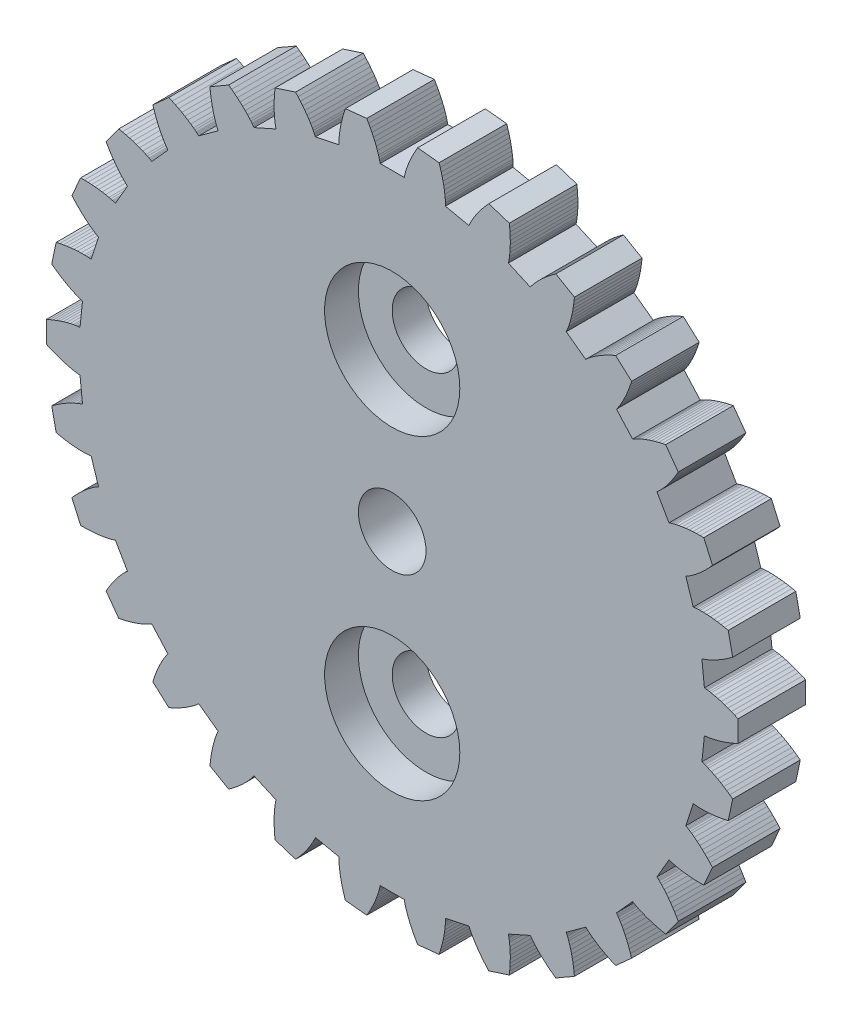
SolidWorks part; units mm, degrees
ref_plane "Front Plane" through (0, 0, 0) normal (0, 0, 1) x (1, 0, 0)
ref_plane "Top Plane" through (0, 0, 0) normal (0, 1, 0) x (1, 0, 0)
ref_plane "Right Plane" through (0, 0, 0) normal (1, 0, 0) x (0, 0, -1)
sketch "Model" plane through (0, 0, 0) normal (0, 0, 1) x (1, 0, 0)
  line L0 (29.209, 16.2732) -> (29.246, 16.2699)
  line L1 (29.246, 16.2699) -> (29.2831, 16.266)
  line L2 (29.2831, 16.266) -> (29.3202, 16.2615)
  line L3 (29.3202, 16.2615) -> (29.3573, 16.2565)
  line L4 (29.3573, 16.2565) -> (29.4317, 16.245)
  line L5 (29.4317, 16.245) -> (29.5061, 16.2317)
  line L6 (29.5061, 16.2317) -> (29.6552, 16.2001)
  line L7 (29.6552, 16.2001) -> (29.8045, 16.1625)
  line L8 (29.8045, 16.1625) -> (29.954, 16.1194)
  line L9 (29.954, 16.1194) -> (30.1035, 16.0712)
  line L10 (30.1035, 16.0712) -> (30.2531, 16.0181)
  line L11 (30.2531, 16.0181) -> (30.4025, 15.9603)
  line L12 (30.4025, 15.9603) -> (30.5519, 15.8981)
  line L13 (30.5519, 15.8981) -> (30.7012, 15.8315)
  line L14 (30.7012, 15.8315) -> (30.7012, 14.8771)
  line L15 (30.7012, 14.8771) -> (30.5519, 14.8105)
  line L16 (30.5519, 14.8105) -> (30.4025, 14.7482)
  line L17 (30.4025, 14.7482) -> (30.2531, 14.6905)
  line L18 (30.2531, 14.6905) -> (30.1035, 14.6374)
  line L19 (30.1035, 14.6374) -> (29.954, 14.5891)
  line L20 (29.954, 14.5891) -> (29.8045, 14.5461)
  line L21 (29.8045, 14.5461) -> (29.6552, 14.5085)
  line L22 (29.6552, 14.5085) -> (29.5061, 14.4769)
  line L23 (29.5061, 14.4769) -> (29.4317, 14.4636)
  line L24 (29.4317, 14.4636) -> (29.3573, 14.4521)
  line L25 (29.3573, 14.4521) -> (29.3202, 14.4471)
  line L26 (29.3202, 14.4471) -> (29.2831, 14.4426)
  line L27 (29.2831, 14.4426) -> (29.246, 14.4387)
  line L28 (29.246, 14.4387) -> (29.209, 14.4354)
  line L29 (29.209, 14.4354) -> (29.0973, 13.3725)
  line L30 (29.0973, 13.3725) -> (29.1328, 13.3616)
  line L31 (29.1328, 13.3616) -> (29.1683, 13.3501)
  line L32 (29.1683, 13.3501) -> (29.2036, 13.338)
  line L33 (29.2036, 13.338) -> (29.2389, 13.3254)
  line L34 (29.2389, 13.3254) -> (29.3092, 13.2987)
  line L35 (29.3092, 13.2987) -> (29.3793, 13.2702)
  line L36 (29.3793, 13.2702) -> (29.5185, 13.2083)
  line L37 (29.5185, 13.2083) -> (29.6568, 13.1405)
  line L38 (29.6568, 13.1405) -> (29.794, 13.0673)
  line L39 (29.794, 13.0673) -> (29.9303, 12.989)
  line L40 (29.9303, 12.989) -> (30.0655, 12.906)
  line L41 (30.0655, 12.906) -> (30.1997, 12.8184)
  line L42 (30.1997, 12.8184) -> (30.3329, 12.7264)
  line L43 (30.3329, 12.7264) -> (30.465, 12.6303)
  line L44 (30.465, 12.6303) -> (30.2666, 11.6967)
  line L45 (30.2666, 11.6967) -> (30.1068, 11.6626)
  line L46 (30.1068, 11.6626) -> (29.9477, 11.6328)
  line L47 (29.9477, 11.6328) -> (29.7895, 11.6074)
  line L48 (29.7895, 11.6074) -> (29.6321, 11.5865)
  line L49 (29.6321, 11.5865) -> (29.4759, 11.5704)
  line L50 (29.4759, 11.5704) -> (29.3207, 11.5594)
  line L51 (29.3207, 11.5594) -> (29.1668, 11.5536)
  line L52 (29.1668, 11.5536) -> (29.0144, 11.5537)
  line L53 (29.0144, 11.5537) -> (28.9389, 11.5562)
  line L54 (28.9389, 11.5562) -> (28.8637, 11.5604)
  line L55 (28.8637, 11.5604) -> (28.8264, 11.5632)
  line L56 (28.8264, 11.5632) -> (28.7892, 11.5666)
  line L57 (28.7892, 11.5666) -> (28.7521, 11.5704)
  line L58 (28.7521, 11.5704) -> (28.7152, 11.5749)
  line L59 (28.7152, 11.5749) -> (28.3849, 10.5585)
  line L60 (28.3849, 10.5585) -> (28.4174, 10.5404)
  line L61 (28.4174, 10.5404) -> (28.4497, 10.5218)
  line L62 (28.4497, 10.5218) -> (28.4818, 10.5026)
  line L63 (28.4818, 10.5026) -> (28.5137, 10.4829)
  line L64 (28.5137, 10.4829) -> (28.5769, 10.4422)
  line L65 (28.5769, 10.4422) -> (28.6395, 10.3998)
  line L66 (28.6395, 10.3998) -> (28.7628, 10.3103)
  line L67 (28.7628, 10.3103) -> (28.884, 10.2152)
  line L68 (28.884, 10.2152) -> (29.003, 10.115)
  line L69 (29.003, 10.115) -> (29.12, 10.0102)
  line L70 (29.12, 10.0102) -> (29.235, 9.9008)
  line L71 (29.235, 9.9008) -> (29.3481, 9.7873)
  line L72 (29.3481, 9.7873) -> (29.4592, 9.6696)
  line L73 (29.4592, 9.6696) -> (29.5684, 9.5481)
  line L74 (29.5684, 9.5481) -> (29.1802, 8.6762)
  line L75 (29.1802, 8.6762) -> (29.0168, 8.6761)
  line L76 (29.0168, 8.6761) -> (28.8551, 8.68)
  line L77 (28.8551, 8.68) -> (28.695, 8.688)
  line L78 (28.695, 8.688) -> (28.5368, 8.7003)
  line L79 (28.5368, 8.7003) -> (28.3806, 8.7171)
  line L80 (28.3806, 8.7171) -> (28.2265, 8.7385)
  line L81 (28.2265, 8.7385) -> (28.0748, 8.7649)
  line L82 (28.0748, 8.7649) -> (27.9257, 8.7967)
  line L83 (27.9257, 8.7967) -> (27.8523, 8.8148)
  line L84 (27.8523, 8.8148) -> (27.7797, 8.8345)
  line L85 (27.7797, 8.8345) -> (27.7438, 8.8451)
  line L86 (27.7438, 8.8451) -> (27.7081, 8.8561)
  line L87 (27.7081, 8.8561) -> (27.6726, 8.8676)
  line L88 (27.6726, 8.8676) -> (27.6375, 8.8796)
  line L89 (27.6375, 8.8796) -> (27.1031, 7.9541)
  line L90 (27.1031, 7.9541) -> (27.1311, 7.9296)
  line L91 (27.1311, 7.9296) -> (27.1588, 7.9047)
  line L92 (27.1588, 7.9047) -> (27.1862, 7.8793)
  line L93 (27.1862, 7.8793) -> (27.2133, 7.8534)
  line L94 (27.2133, 7.8534) -> (27.2667, 7.8004)
  line L95 (27.2667, 7.8004) -> (27.3191, 7.7459)
  line L96 (27.3191, 7.7459) -> (27.4211, 7.6327)
  line L97 (27.4211, 7.6327) -> (27.5198, 7.5145)
  line L98 (27.5198, 7.5145) -> (27.6154, 7.3918)
  line L99 (27.6154, 7.3918) -> (27.708, 7.2649)
  line L100 (27.708, 7.2649) -> (27.7978, 7.134)
  line L101 (27.7978, 7.134) -> (27.8848, 6.9994)
  line L102 (27.8848, 6.9994) -> (27.9691, 6.8613)
  line L103 (27.9691, 6.8613) -> (28.0507, 6.7197)
  line L104 (28.0507, 6.7197) -> (27.4897, 5.9476)
  line L105 (27.4897, 5.9476) -> (27.3298, 5.9814)
  line L106 (27.3298, 5.9814) -> (27.1724, 6.0188)
  line L107 (27.1724, 6.0188) -> (27.0175, 6.06)
  line L108 (27.0175, 6.06) -> (26.8653, 6.1049)
  line L109 (26.8653, 6.1049) -> (26.7159, 6.1538)
  line L110 (26.7159, 6.1538) -> (26.5697, 6.2068)
  line L111 (26.5697, 6.2068) -> (26.4268, 6.2641)
  line L112 (26.4268, 6.2641) -> (26.2876, 6.3262)
  line L113 (26.2876, 6.3262) -> (26.2196, 6.3592)
  line L114 (26.2196, 6.3592) -> (26.1527, 6.3936)
  line L115 (26.1527, 6.3936) -> (26.1197, 6.4114)
  line L116 (26.1197, 6.4114) -> (26.0871, 6.4296)
  line L117 (26.0871, 6.4296) -> (26.0548, 6.4482)
  line L118 (26.0548, 6.4482) -> (26.0229, 6.4673)
  line L119 (26.0229, 6.4673) -> (25.3078, 5.6731)
  line L120 (25.3078, 5.6731) -> (25.3301, 5.6433)
  line L121 (25.3301, 5.6433) -> (25.352, 5.6132)
  line L122 (25.352, 5.6132) -> (25.3735, 5.5826)
  line L123 (25.3735, 5.5826) -> (25.3946, 5.5517)
  line L124 (25.3946, 5.5517) -> (25.4358, 5.4888)
  line L125 (25.4358, 5.4888) -> (25.4757, 5.4245)
  line L126 (25.4757, 5.4245) -> (25.552, 5.2926)
  line L127 (25.552, 5.2926) -> (25.624, 5.1565)
  line L128 (25.624, 5.1565) -> (25.692, 5.0166)
  line L129 (25.692, 5.0166) -> (25.7562, 4.8732)
  line L130 (25.7562, 4.8732) -> (25.8168, 4.7265)
  line L131 (25.8168, 4.7265) -> (25.8739, 4.5768)
  line L132 (25.8739, 4.5768) -> (25.9276, 4.4241)
  line L133 (25.9276, 4.4241) -> (25.978, 4.2687)
  line L134 (25.978, 4.2687) -> (25.2687, 3.63)
  line L135 (25.2687, 3.63) -> (25.1194, 3.6964)
  line L136 (25.1194, 3.6964) -> (24.9732, 3.7657)
  line L137 (24.9732, 3.7657) -> (24.8302, 3.8382)
  line L138 (24.8302, 3.8382) -> (24.6907, 3.9138)
  line L139 (24.6907, 3.9138) -> (24.5548, 3.9926)
  line L140 (24.5548, 3.9926) -> (24.4227, 4.0749)
  line L141 (24.4227, 4.0749) -> (24.2949, 4.1607)
  line L142 (24.2949, 4.1607) -> (24.1717, 4.2503)
  line L143 (24.1717, 4.2503) -> (24.112, 4.2968)
  line L144 (24.112, 4.2968) -> (24.0537, 4.3443)
  line L145 (24.0537, 4.3443) -> (24.0251, 4.3685)
  line L146 (24.0251, 4.3685) -> (23.997, 4.3931)
  line L147 (23.997, 4.3931) -> (23.9693, 4.4181)
  line L148 (23.9693, 4.4181) -> (23.9421, 4.4434)
  line L149 (23.9421, 4.4434) -> (23.0774, 3.8152)
  line L150 (23.0774, 3.8152) -> (23.0931, 3.7815)
  line L151 (23.0931, 3.7815) -> (23.1082, 3.7474)
  line L152 (23.1082, 3.7474) -> (23.1229, 3.7131)
  line L153 (23.1229, 3.7131) -> (23.1371, 3.6784)
  line L154 (23.1371, 3.6784) -> (23.1644, 3.6083)
  line L155 (23.1644, 3.6083) -> (23.19, 3.5372)
  line L156 (23.19, 3.5372) -> (23.2372, 3.3922)
  line L157 (23.2372, 3.3922) -> (23.2793, 3.2441)
  line L158 (23.2793, 3.2441) -> (23.3168, 3.0932)
  line L159 (23.3168, 3.0932) -> (23.3498, 2.9395)
  line L160 (23.3498, 2.9395) -> (23.3785, 2.7835)
  line L161 (23.3785, 2.7835) -> (23.4033, 2.6251)
  line L162 (23.4033, 2.6251) -> (23.4241, 2.4646)
  line L163 (23.4241, 2.4646) -> (23.441, 2.3021)
  line L164 (23.441, 2.3021) -> (22.6144, 1.8249)
  line L165 (22.6144, 1.8249) -> (22.4822, 1.9208)
  line L166 (22.4822, 1.9208) -> (22.3536, 2.0191)
  line L167 (22.3536, 2.0191) -> (22.2288, 2.1197)
  line L168 (22.2288, 2.1197) -> (22.108, 2.2226)
  line L169 (22.108, 2.2226) -> (21.9915, 2.328)
  line L170 (21.9915, 2.328) -> (21.8795, 2.4359)
  line L171 (21.8795, 2.4359) -> (21.7722, 2.5464)
  line L172 (21.7722, 2.5464) -> (21.6703, 2.6598)
  line L173 (21.6703, 2.6598) -> (21.6216, 2.7176)
  line L174 (21.6216, 2.7176) -> (21.5745, 2.7762)
  line L175 (21.5745, 2.7762) -> (21.5516, 2.8058)
  line L176 (21.5516, 2.8058) -> (21.5292, 2.8357)
  line L177 (21.5292, 2.8357) -> (21.5072, 2.8659)
  line L178 (21.5072, 2.8659) -> (21.4859, 2.8963)
  line L179 (21.4859, 2.8963) -> (20.5095, 2.4616)
  line L180 (20.5095, 2.4616) -> (20.5178, 2.4254)
  line L181 (20.5178, 2.4254) -> (20.5256, 2.3889)
  line L182 (20.5256, 2.3889) -> (20.5328, 2.3523)
  line L183 (20.5328, 2.3523) -> (20.5395, 2.3154)
  line L184 (20.5395, 2.3154) -> (20.5516, 2.2411)
  line L185 (20.5516, 2.2411) -> (20.5619, 2.1662)
  line L186 (20.5619, 2.1662) -> (20.5779, 2.0147)
  line L187 (20.5779, 2.0147) -> (20.5883, 1.8611)
  line L188 (20.5883, 1.8611) -> (20.5935, 1.7056)
  line L189 (20.5935, 1.7056) -> (20.5939, 1.5485)
  line L190 (20.5939, 1.5485) -> (20.5896, 1.3898)
  line L191 (20.5896, 1.3898) -> (20.5808, 1.2298)
  line L192 (20.5808, 1.2298) -> (20.5678, 1.0685)
  line L193 (20.5678, 1.0685) -> (20.5506, 0.906)
  line L194 (20.5506, 0.906) -> (19.6429, 0.6111)
  line L195 (19.6429, 0.6111) -> (19.5334, 0.7324)
  line L196 (19.5334, 0.7324) -> (19.4281, 0.8553)
  line L197 (19.4281, 0.8553) -> (19.3269, 0.9796)
  line L198 (19.3269, 0.9796) -> (19.2302, 1.1054)
  line L199 (19.2302, 1.1054) -> (19.1381, 1.2327)
  line L200 (19.1381, 1.2327) -> (19.051, 1.3615)
  line L201 (19.051, 1.3615) -> (18.9691, 1.4919)
  line L202 (18.9691, 1.4919) -> (18.893, 1.624)
  line L203 (18.893, 1.624) -> (18.8573, 1.6907)
  line L204 (18.8573, 1.6907) -> (18.8234, 1.7578)
  line L205 (18.8234, 1.7578) -> (18.8072, 1.7916)
  line L206 (18.8072, 1.7916) -> (18.7915, 1.8255)
  line L207 (18.7915, 1.8255) -> (18.7763, 1.8595)
  line L208 (18.7763, 1.8595) -> (18.7617, 1.8937)
  line L209 (18.7617, 1.8937) -> (17.7163, 1.6715)
  line L210 (17.7163, 1.6715) -> (17.7169, 1.6343)
  line L211 (17.7169, 1.6343) -> (17.7169, 1.5971)
  line L212 (17.7169, 1.5971) -> (17.7164, 1.5597)
  line L213 (17.7164, 1.5597) -> (17.7153, 1.5223)
  line L214 (17.7153, 1.5223) -> (17.7116, 1.4471)
  line L215 (17.7116, 1.4471) -> (17.7061, 1.3717)
  line L216 (17.7061, 1.3717) -> (17.6903, 1.2201)
  line L217 (17.6903, 1.2201) -> (17.6685, 1.0677)
  line L218 (17.6685, 1.0677) -> (17.6413, 0.9146)
  line L219 (17.6413, 0.9146) -> (17.609, 0.7608)
  line L220 (17.609, 0.7608) -> (17.5718, 0.6065)
  line L221 (17.5718, 0.6065) -> (17.53, 0.4518)
  line L222 (17.53, 0.4518) -> (17.4837, 0.2967)
  line L223 (17.4837, 0.2967) -> (17.4331, 0.1414)
  line L224 (17.4331, 0.1414) -> (16.4839, 0.0416)
  line L225 (16.4839, 0.0416) -> (16.402, 0.183)
  line L226 (16.402, 0.183) -> (16.3245, 0.3251)
  line L227 (16.3245, 0.3251) -> (16.2515, 0.4677)
  line L228 (16.2515, 0.4677) -> (16.183, 0.6109)
  line L229 (16.183, 0.6109) -> (16.1194, 0.7546)
  line L230 (16.1194, 0.7546) -> (16.0609, 0.8987)
  line L231 (16.0609, 0.8987) -> (16.008, 1.0433)
  line L232 (16.008, 1.0433) -> (15.961, 1.1883)
  line L233 (15.961, 1.1883) -> (15.9399, 1.2609)
  line L234 (15.9399, 1.2609) -> (15.9207, 1.3336)
  line L235 (15.9207, 1.3336) -> (15.9119, 1.3701)
  line L236 (15.9119, 1.3701) -> (15.9036, 1.4065)
  line L237 (15.9036, 1.4065) -> (15.8958, 1.4429)
  line L238 (15.8958, 1.4429) -> (15.8887, 1.4794)
  line L239 (15.8887, 1.4794) -> (14.8199, 1.4794)
  line L240 (14.8199, 1.4794) -> (14.8128, 1.4429)
  line L241 (14.8128, 1.4429) -> (14.805, 1.4065)
  line L242 (14.805, 1.4065) -> (14.7967, 1.3701)
  line L243 (14.7967, 1.3701) -> (14.7878, 1.3336)
  line L244 (14.7878, 1.3336) -> (14.7686, 1.2609)
  line L245 (14.7686, 1.2609) -> (14.7476, 1.1883)
  line L246 (14.7476, 1.1883) -> (14.7006, 1.0433)
  line L247 (14.7006, 1.0433) -> (14.6476, 0.8987)
  line L248 (14.6476, 0.8987) -> (14.5891, 0.7546)
  line L249 (14.5891, 0.7546) -> (14.5256, 0.6109)
  line L250 (14.5256, 0.6109) -> (14.4571, 0.4677)
  line L251 (14.4571, 0.4677) -> (14.384, 0.3251)
  line L252 (14.384, 0.3251) -> (14.3065, 0.183)
  line L253 (14.3065, 0.183) -> (14.2247, 0.0416)
  line L254 (14.2247, 0.0416) -> (13.2755, 0.1414)
  line L255 (13.2755, 0.1414) -> (13.2249, 0.2967)
  line L256 (13.2249, 0.2967) -> (13.1786, 0.4518)
  line L257 (13.1786, 0.4518) -> (13.1368, 0.6065)
  line L258 (13.1368, 0.6065) -> (13.0996, 0.7608)
  line L259 (13.0996, 0.7608) -> (13.0673, 0.9146)
  line L260 (13.0673, 0.9146) -> (13.04, 1.0677)
  line L261 (13.04, 1.0677) -> (13.0183, 1.2201)
  line L262 (13.0183, 1.2201) -> (13.0024, 1.3717)
  line L263 (13.0024, 1.3717) -> (12.997, 1.4471)
  line L264 (12.997, 1.4471) -> (12.9933, 1.5223)
  line L265 (12.9933, 1.5223) -> (12.9922, 1.5597)
  line L266 (12.9922, 1.5597) -> (12.9916, 1.5971)
  line L267 (12.9916, 1.5971) -> (12.9916, 1.6343)
  line L268 (12.9916, 1.6343) -> (12.9922, 1.6715)
  line L269 (12.9922, 1.6715) -> (11.9468, 1.8937)
  line L270 (11.9468, 1.8937) -> (11.9323, 1.8595)
  line L271 (11.9323, 1.8595) -> (11.9171, 1.8255)
  line L272 (11.9171, 1.8255) -> (11.9014, 1.7916)
  line L273 (11.9014, 1.7916) -> (11.8852, 1.7578)
  line L274 (11.8852, 1.7578) -> (11.8513, 1.6907)
  line L275 (11.8513, 1.6907) -> (11.8156, 1.624)
  line L276 (11.8156, 1.624) -> (11.7395, 1.4919)
  line L277 (11.7395, 1.4919) -> (11.6576, 1.3615)
  line L278 (11.6576, 1.3615) -> (11.5704, 1.2327)
  line L279 (11.5704, 1.2327) -> (11.4783, 1.1054)
  line L280 (11.4783, 1.1054) -> (11.3816, 0.9796)
  line L281 (11.3816, 0.9796) -> (11.2805, 0.8553)
  line L282 (11.2805, 0.8553) -> (11.1751, 0.7324)
  line L283 (11.1751, 0.7324) -> (11.0657, 0.6111)
  line L284 (11.0657, 0.6111) -> (10.158, 0.906)
  line L285 (10.158, 0.906) -> (10.1408, 1.0685)
  line L286 (10.1408, 1.0685) -> (10.1277, 1.2298)
  line L287 (10.1277, 1.2298) -> (10.119, 1.3898)
  line L288 (10.119, 1.3898) -> (10.1147, 1.5485)
  line L289 (10.1147, 1.5485) -> (10.115, 1.7056)
  line L290 (10.115, 1.7056) -> (10.1203, 1.8611)
  line L291 (10.1203, 1.8611) -> (10.1306, 2.0147)
  line L292 (10.1306, 2.0147) -> (10.1467, 2.1662)
  line L293 (10.1467, 2.1662) -> (10.157, 2.2411)
  line L294 (10.157, 2.2411) -> (10.1691, 2.3154)
  line L295 (10.1691, 2.3154) -> (10.1758, 2.3523)
  line L296 (10.1758, 2.3523) -> (10.183, 2.3889)
  line L297 (10.183, 2.3889) -> (10.1907, 2.4254)
  line L298 (10.1907, 2.4254) -> (10.199, 2.4616)
  line L299 (10.199, 2.4616) -> (9.2227, 2.8963)
  line L300 (9.2227, 2.8963) -> (9.2013, 2.8659)
  line L301 (9.2013, 2.8659) -> (9.1794, 2.8357)
  line L302 (9.1794, 2.8357) -> (9.157, 2.8058)
  line L303 (9.157, 2.8058) -> (9.1341, 2.7762)
  line L304 (9.1341, 2.7762) -> (9.087, 2.7176)
  line L305 (9.087, 2.7176) -> (9.0382, 2.6598)
  line L306 (9.0382, 2.6598) -> (8.9363, 2.5464)
  line L307 (8.9363, 2.5464) -> (8.8291, 2.4359)
  line L308 (8.8291, 2.4359) -> (8.7171, 2.328)
  line L309 (8.7171, 2.328) -> (8.6005, 2.2226)
  line L310 (8.6005, 2.2226) -> (8.4798, 2.1197)
  line L311 (8.4798, 2.1197) -> (8.355, 2.0191)
  line L312 (8.355, 2.0191) -> (8.2264, 1.9208)
  line L313 (8.2264, 1.9208) -> (8.0941, 1.8249)
  line L314 (8.0941, 1.8249) -> (7.2676, 2.3021)
  line L315 (7.2676, 2.3021) -> (7.2845, 2.4646)
  line L316 (7.2845, 2.4646) -> (7.3053, 2.6251)
  line L317 (7.3053, 2.6251) -> (7.33, 2.7835)
  line L318 (7.33, 2.7835) -> (7.3588, 2.9395)
  line L319 (7.3588, 2.9395) -> (7.3918, 3.0932)
  line L320 (7.3918, 3.0932) -> (7.4292, 3.2441)
  line L321 (7.4292, 3.2441) -> (7.4713, 3.3922)
  line L322 (7.4713, 3.3922) -> (7.5185, 3.5372)
  line L323 (7.5185, 3.5372) -> (7.5442, 3.6083)
  line L324 (7.5442, 3.6083) -> (7.5714, 3.6784)
  line L325 (7.5714, 3.6784) -> (7.5857, 3.7131)
  line L326 (7.5857, 3.7131) -> (7.6003, 3.7474)
  line L327 (7.6003, 3.7474) -> (7.6155, 3.7815)
  line L328 (7.6155, 3.7815) -> (7.6312, 3.8152)
  line L329 (7.6312, 3.8152) -> (6.7665, 4.4434)
  line L330 (6.7665, 4.4434) -> (6.7393, 4.4181)
  line L331 (6.7393, 4.4181) -> (6.7116, 4.3931)
  line L332 (6.7116, 4.3931) -> (6.6835, 4.3685)
  line L333 (6.6835, 4.3685) -> (6.6549, 4.3443)
  line L334 (6.6549, 4.3443) -> (6.5966, 4.2968)
  line L335 (6.5966, 4.2968) -> (6.5369, 4.2503)
  line L336 (6.5369, 4.2503) -> (6.4137, 4.1607)
  line L337 (6.4137, 4.1607) -> (6.2858, 4.0749)
  line L338 (6.2858, 4.0749) -> (6.1538, 3.9926)
  line L339 (6.1538, 3.9926) -> (6.0179, 3.9138)
  line L340 (6.0179, 3.9138) -> (5.8784, 3.8382)
  line L341 (5.8784, 3.8382) -> (5.7354, 3.7657)
  line L342 (5.7354, 3.7657) -> (5.5892, 3.6964)
  line L343 (5.5892, 3.6964) -> (5.4399, 3.63)
  line L344 (5.4399, 3.63) -> (4.7306, 4.2687)
  line L345 (4.7306, 4.2687) -> (4.7809, 4.4241)
  line L346 (4.7809, 4.4241) -> (4.8346, 4.5768)
  line L347 (4.8346, 4.5768) -> (4.8918, 4.7265)
  line L348 (4.8918, 4.7265) -> (4.9524, 4.8732)
  line L349 (4.9524, 4.8732) -> (5.0166, 5.0166)
  line L350 (5.0166, 5.0166) -> (5.0846, 5.1565)
  line L351 (5.0846, 5.1565) -> (5.1565, 5.2926)
  line L352 (5.1565, 5.2926) -> (5.2328, 5.4245)
  line L353 (5.2328, 5.4245) -> (5.2728, 5.4888)
  line L354 (5.2728, 5.4888) -> (5.314, 5.5517)
  line L355 (5.314, 5.5517) -> (5.3351, 5.5826)
  line L356 (5.3351, 5.5826) -> (5.3566, 5.6132)
  line L357 (5.3566, 5.6132) -> (5.3785, 5.6433)
  line L358 (5.3785, 5.6433) -> (5.4008, 5.6731)
  line L359 (5.4008, 5.6731) -> (4.6857, 6.4673)
  line L360 (4.6857, 6.4673) -> (4.6538, 6.4482)
  line L361 (4.6538, 6.4482) -> (4.6215, 6.4296)
  line L362 (4.6215, 6.4296) -> (4.5889, 6.4114)
  line L363 (4.5889, 6.4114) -> (4.5559, 6.3936)
  line L364 (4.5559, 6.3936) -> (4.489, 6.3592)
  line L365 (4.489, 6.3592) -> (4.4209, 6.3262)
  line L366 (4.4209, 6.3262) -> (4.2818, 6.2641)
  line L367 (4.2818, 6.2641) -> (4.1389, 6.2068)
  line L368 (4.1389, 6.2068) -> (3.9926, 6.1538)
  line L369 (3.9926, 6.1538) -> (3.8433, 6.1049)
  line L370 (3.8433, 6.1049) -> (3.6911, 6.06)
  line L371 (3.6911, 6.06) -> (3.5362, 6.0188)
  line L372 (3.5362, 6.0188) -> (3.3788, 5.9814)
  line L373 (3.3788, 5.9814) -> (3.2189, 5.9476)
  line L374 (3.2189, 5.9476) -> (2.6579, 6.7197)
  line L375 (2.6579, 6.7197) -> (2.7395, 6.8613)
  line L376 (2.7395, 6.8613) -> (2.8238, 6.9994)
  line L377 (2.8238, 6.9994) -> (2.9108, 7.134)
  line L378 (2.9108, 7.134) -> (3.0005, 7.2649)
  line L379 (3.0005, 7.2649) -> (3.0932, 7.3918)
  line L380 (3.0932, 7.3918) -> (3.1887, 7.5145)
  line L381 (3.1887, 7.5145) -> (3.2875, 7.6327)
  line L382 (3.2875, 7.6327) -> (3.3895, 7.7459)
  line L383 (3.3895, 7.7459) -> (3.4419, 7.8004)
  line L384 (3.4419, 7.8004) -> (3.4953, 7.8534)
  line L385 (3.4953, 7.8534) -> (3.5224, 7.8793)
  line L386 (3.5224, 7.8793) -> (3.5498, 7.9047)
  line L387 (3.5498, 7.9047) -> (3.5775, 7.9296)
  line L388 (3.5775, 7.9296) -> (3.6055, 7.9541)
  line L389 (3.6055, 7.9541) -> (3.0711, 8.8796)
  line L390 (3.0711, 8.8796) -> (3.0359, 8.8676)
  line L391 (3.0359, 8.8676) -> (3.0005, 8.8561)
  line L392 (3.0005, 8.8561) -> (2.9648, 8.8451)
  line L393 (2.9648, 8.8451) -> (2.9288, 8.8345)
  line L394 (2.9288, 8.8345) -> (2.8562, 8.8148)
  line L395 (2.8562, 8.8148) -> (2.7828, 8.7967)
  line L396 (2.7828, 8.7967) -> (2.6338, 8.7649)
  line L397 (2.6338, 8.7649) -> (2.4821, 8.7385)
  line L398 (2.4821, 8.7385) -> (2.328, 8.7171)
  line L399 (2.328, 8.7171) -> (2.1718, 8.7003)
  line L400 (2.1718, 8.7003) -> (2.0136, 8.688)
  line L401 (2.0136, 8.688) -> (1.8535, 8.68)
  line L402 (1.8535, 8.68) -> (1.6917, 8.6761)
  line L403 (1.6917, 8.6761) -> (1.5283, 8.6762)
  line L404 (1.5283, 8.6762) -> (1.1401, 9.5481)
  line L405 (1.1401, 9.5481) -> (1.2494, 9.6696)
  line L406 (1.2494, 9.6696) -> (1.3605, 9.7873)
  line L407 (1.3605, 9.7873) -> (1.4736, 9.9008)
  line L408 (1.4736, 9.9008) -> (1.5886, 10.0102)
  line L409 (1.5886, 10.0102) -> (1.7056, 10.115)
  line L410 (1.7056, 10.115) -> (1.8246, 10.2152)
  line L411 (1.8246, 10.2152) -> (1.9457, 10.3103)
  line L412 (1.9457, 10.3103) -> (2.0691, 10.3998)
  line L413 (2.0691, 10.3998) -> (2.1317, 10.4422)
  line L414 (2.1317, 10.4422) -> (2.1949, 10.4829)
  line L415 (2.1949, 10.4829) -> (2.2268, 10.5026)
  line L416 (2.2268, 10.5026) -> (2.2589, 10.5218)
  line L417 (2.2589, 10.5218) -> (2.2911, 10.5404)
  line L418 (2.2911, 10.5404) -> (2.3236, 10.5585)
  line L419 (2.3236, 10.5585) -> (1.9934, 11.5749)
  line L420 (1.9934, 11.5749) -> (1.9565, 11.5704)
  line L421 (1.9565, 11.5704) -> (1.9194, 11.5666)
  line L422 (1.9194, 11.5666) -> (1.8822, 11.5632)
  line L423 (1.8822, 11.5632) -> (1.8448, 11.5604)
  line L424 (1.8448, 11.5604) -> (1.7697, 11.5562)
  line L425 (1.7697, 11.5562) -> (1.6941, 11.5537)
  line L426 (1.6941, 11.5537) -> (1.5417, 11.5536)
  line L427 (1.5417, 11.5536) -> (1.3879, 11.5594)
  line L428 (1.3879, 11.5594) -> (1.2327, 11.5704)
  line L429 (1.2327, 11.5704) -> (1.0764, 11.5865)
  line L430 (1.0764, 11.5865) -> (0.9191, 11.6074)
  line L431 (0.9191, 11.6074) -> (0.7609, 11.6328)
  line L432 (0.7609, 11.6328) -> (0.6018, 11.6626)
  line L433 (0.6018, 11.6626) -> (0.442, 11.6967)
  line L434 (0.442, 11.6967) -> (0.2436, 12.6303)
  line L435 (0.2436, 12.6303) -> (0.3757, 12.7264)
  line L436 (0.3757, 12.7264) -> (0.5089, 12.8184)
  line L437 (0.5089, 12.8184) -> (0.6431, 12.906)
  line L438 (0.6431, 12.906) -> (0.7783, 12.989)
  line L439 (0.7783, 12.989) -> (0.9146, 13.0673)
  line L440 (0.9146, 13.0673) -> (1.0518, 13.1405)
  line L441 (1.0518, 13.1405) -> (1.19, 13.2083)
  line L442 (1.19, 13.2083) -> (1.3293, 13.2702)
  line L443 (1.3293, 13.2702) -> (1.3993, 13.2987)
  line L444 (1.3993, 13.2987) -> (1.4697, 13.3254)
  line L445 (1.4697, 13.3254) -> (1.5049, 13.338)
  line L446 (1.5049, 13.338) -> (1.5403, 13.3501)
  line L447 (1.5403, 13.3501) -> (1.5757, 13.3616)
  line L448 (1.5757, 13.3616) -> (1.6113, 13.3725)
  line L449 (1.6113, 13.3725) -> (1.4996, 14.4354)
  line L450 (1.4996, 14.4354) -> (1.4625, 14.4387)
  line L451 (1.4625, 14.4387) -> (1.4255, 14.4426)
  line L452 (1.4255, 14.4426) -> (1.3884, 14.4471)
  line L453 (1.3884, 14.4471) -> (1.3512, 14.4521)
  line L454 (1.3512, 14.4521) -> (1.2769, 14.4636)
  line L455 (1.2769, 14.4636) -> (1.2025, 14.4769)
  line L456 (1.2025, 14.4769) -> (1.0534, 14.5085)
  line L457 (1.0534, 14.5085) -> (0.9041, 14.5461)
  line L458 (0.9041, 14.5461) -> (0.7546, 14.5891)
  line L459 (0.7546, 14.5891) -> (0.6051, 14.6374)
  line L460 (0.6051, 14.6374) -> (0.4555, 14.6905)
  line L461 (0.4555, 14.6905) -> (0.306, 14.7482)
  line L462 (0.306, 14.7482) -> (0.1566, 14.8105)
  line L463 (0.1566, 14.8105) -> (0.0074, 14.8771)
  line L464 (0.0074, 14.8771) -> (0.0074, 15.8315)
  line L465 (0.0074, 15.8315) -> (0.1566, 15.8981)
  line L466 (0.1566, 15.8981) -> (0.306, 15.9603)
  line L467 (0.306, 15.9603) -> (0.4555, 16.0181)
  line L468 (0.4555, 16.0181) -> (0.6051, 16.0712)
  line L469 (0.6051, 16.0712) -> (0.7546, 16.1194)
  line L470 (0.7546, 16.1194) -> (0.9041, 16.1625)
  line L471 (0.9041, 16.1625) -> (1.0534, 16.2001)
  line L472 (1.0534, 16.2001) -> (1.2025, 16.2317)
  line L473 (1.2025, 16.2317) -> (1.2769, 16.245)
  line L474 (1.2769, 16.245) -> (1.3512, 16.2565)
  line L475 (1.3512, 16.2565) -> (1.3884, 16.2615)
  line L476 (1.3884, 16.2615) -> (1.4255, 16.266)
  line L477 (1.4255, 16.266) -> (1.4625, 16.2699)
  line L478 (1.4625, 16.2699) -> (1.4996, 16.2732)
  line L479 (1.4996, 16.2732) -> (1.6113, 17.3361)
  line L480 (1.6113, 17.3361) -> (1.5757, 17.347)
  line L481 (1.5757, 17.347) -> (1.5403, 17.3585)
  line L482 (1.5403, 17.3585) -> (1.5049, 17.3706)
  line L483 (1.5049, 17.3706) -> (1.4697, 17.3832)
  line L484 (1.4697, 17.3832) -> (1.3993, 17.4099)
  line L485 (1.3993, 17.4099) -> (1.3293, 17.4384)
  line L486 (1.3293, 17.4384) -> (1.19, 17.5003)
  line L487 (1.19, 17.5003) -> (1.0518, 17.5681)
  line L488 (1.0518, 17.5681) -> (0.9146, 17.6413)
  line L489 (0.9146, 17.6413) -> (0.7783, 17.7196)
  line L490 (0.7783, 17.7196) -> (0.6431, 17.8026)
  line L491 (0.6431, 17.8026) -> (0.5089, 17.8902)
  line L492 (0.5089, 17.8902) -> (0.3757, 17.9821)
  line L493 (0.3757, 17.9821) -> (0.2436, 18.0783)
  line L494 (0.2436, 18.0783) -> (0.442, 19.0119)
  line L495 (0.442, 19.0119) -> (0.6018, 19.046)
  line L496 (0.6018, 19.046) -> (0.7609, 19.0758)
  line L497 (0.7609, 19.0758) -> (0.9191, 19.1012)
  line L498 (0.9191, 19.1012) -> (1.0764, 19.1221)
  line L499 (1.0764, 19.1221) -> (1.2327, 19.1381)
  line L500 (1.2327, 19.1381) -> (1.3879, 19.1492)
  line L501 (1.3879, 19.1492) -> (1.5417, 19.1549)
  line L502 (1.5417, 19.1549) -> (1.6941, 19.1548)
  line L503 (1.6941, 19.1548) -> (1.7697, 19.1524)
  line L504 (1.7697, 19.1524) -> (1.8448, 19.1482)
  line L505 (1.8448, 19.1482) -> (1.8822, 19.1453)
  line L506 (1.8822, 19.1453) -> (1.9194, 19.142)
  line L507 (1.9194, 19.142) -> (1.9565, 19.1381)
  line L508 (1.9565, 19.1381) -> (1.9934, 19.1336)
  line L509 (1.9934, 19.1336) -> (2.3236, 20.1501)
  line L510 (2.3236, 20.1501) -> (2.2911, 20.1681)
  line L511 (2.2911, 20.1681) -> (2.2589, 20.1868)
  line L512 (2.2589, 20.1868) -> (2.2268, 20.206)
  line L513 (2.2268, 20.206) -> (2.1949, 20.2256)
  line L514 (2.1949, 20.2256) -> (2.1317, 20.2664)
  line L515 (2.1317, 20.2664) -> (2.0691, 20.3088)
  line L516 (2.0691, 20.3088) -> (1.9457, 20.3983)
  line L517 (1.9457, 20.3983) -> (1.8246, 20.4934)
  line L518 (1.8246, 20.4934) -> (1.7056, 20.5935)
  line L519 (1.7056, 20.5935) -> (1.5886, 20.6984)
  line L520 (1.5886, 20.6984) -> (1.4736, 20.8077)
  line L521 (1.4736, 20.8077) -> (1.3605, 20.9213)
  line L522 (1.3605, 20.9213) -> (1.2494, 21.0389)
  line L523 (1.2494, 21.0389) -> (1.1401, 21.1605)
  line L524 (1.1401, 21.1605) -> (1.5283, 22.0324)
  line L525 (1.5283, 22.0324) -> (1.6917, 22.0325)
  line L526 (1.6917, 22.0325) -> (1.8535, 22.0286)
  line L527 (1.8535, 22.0286) -> (2.0136, 22.0206)
  line L528 (2.0136, 22.0206) -> (2.1718, 22.0083)
  line L529 (2.1718, 22.0083) -> (2.328, 21.9915)
  line L530 (2.328, 21.9915) -> (2.4821, 21.9701)
  line L531 (2.4821, 21.9701) -> (2.6338, 21.9437)
  line L532 (2.6338, 21.9437) -> (2.7828, 21.9119)
  line L533 (2.7828, 21.9119) -> (2.8562, 21.8938)
  line L534 (2.8562, 21.8938) -> (2.9288, 21.874)
  line L535 (2.9288, 21.874) -> (2.9648, 21.8635)
  line L536 (2.9648, 21.8635) -> (3.0005, 21.8525)
  line L537 (3.0005, 21.8525) -> (3.0359, 21.841)
  line L538 (3.0359, 21.841) -> (3.0711, 21.8289)
  line L539 (3.0711, 21.8289) -> (3.6055, 22.7545)
  line L540 (3.6055, 22.7545) -> (3.5775, 22.7789)
  line L541 (3.5775, 22.7789) -> (3.5498, 22.8039)
  line L542 (3.5498, 22.8039) -> (3.5224, 22.8293)
  line L543 (3.5224, 22.8293) -> (3.4953, 22.8552)
  line L544 (3.4953, 22.8552) -> (3.4419, 22.9082)
  line L545 (3.4419, 22.9082) -> (3.3895, 22.9627)
  line L546 (3.3895, 22.9627) -> (3.2875, 23.0759)
  line L547 (3.2875, 23.0759) -> (3.1887, 23.194)
  line L548 (3.1887, 23.194) -> (3.0932, 23.3168)
  line L549 (3.0932, 23.3168) -> (3.0005, 23.4437)
  line L550 (3.0005, 23.4437) -> (2.9108, 23.5745)
  line L551 (2.9108, 23.5745) -> (2.8238, 23.7091)
  line L552 (2.8238, 23.7091) -> (2.7395, 23.8473)
  line L553 (2.7395, 23.8473) -> (2.6579, 23.9889)
  line L554 (2.6579, 23.9889) -> (3.2189, 24.761)
  line L555 (3.2189, 24.761) -> (3.3788, 24.7272)
  line L556 (3.3788, 24.7272) -> (3.5362, 24.6897)
  line L557 (3.5362, 24.6897) -> (3.6911, 24.6486)
  line L558 (3.6911, 24.6486) -> (3.8433, 24.6037)
  line L559 (3.8433, 24.6037) -> (3.9926, 24.5548)
  line L560 (3.9926, 24.5548) -> (4.1389, 24.5018)
  line L561 (4.1389, 24.5018) -> (4.2818, 24.4444)
  line L562 (4.2818, 24.4444) -> (4.4209, 24.3823)
  line L563 (4.4209, 24.3823) -> (4.489, 24.3494)
  line L564 (4.489, 24.3494) -> (4.5559, 24.315)
  line L565 (4.5559, 24.315) -> (4.5889, 24.2972)
  line L566 (4.5889, 24.2972) -> (4.6215, 24.279)
  line L567 (4.6215, 24.279) -> (4.6538, 24.2604)
  line L568 (4.6538, 24.2604) -> (4.6857, 24.2413)
  line L569 (4.6857, 24.2413) -> (5.4008, 25.0355)
  line L570 (5.4008, 25.0355) -> (5.3785, 25.0652)
  line L571 (5.3785, 25.0652) -> (5.3566, 25.0954)
  line L572 (5.3566, 25.0954) -> (5.3351, 25.1259)
  line L573 (5.3351, 25.1259) -> (5.314, 25.1569)
  line L574 (5.314, 25.1569) -> (5.2728, 25.2198)
  line L575 (5.2728, 25.2198) -> (5.2328, 25.284)
  line L576 (5.2328, 25.284) -> (5.1565, 25.416)
  line L577 (5.1565, 25.416) -> (5.0846, 25.5521)
  line L578 (5.0846, 25.5521) -> (5.0166, 25.692)
  line L579 (5.0166, 25.692) -> (4.9524, 25.8354)
  line L580 (4.9524, 25.8354) -> (4.8918, 25.9821)
  line L581 (4.8918, 25.9821) -> (4.8346, 26.1318)
  line L582 (4.8346, 26.1318) -> (4.7809, 26.2845)
  line L583 (4.7809, 26.2845) -> (4.7306, 26.4399)
  line L584 (4.7306, 26.4399) -> (5.4399, 27.0785)
  line L585 (5.4399, 27.0785) -> (5.5892, 27.0122)
  line L586 (5.5892, 27.0122) -> (5.7354, 26.9429)
  line L587 (5.7354, 26.9429) -> (5.8784, 26.8704)
  line L588 (5.8784, 26.8704) -> (6.0179, 26.7948)
  line L589 (6.0179, 26.7948) -> (6.1538, 26.7159)
  line L590 (6.1538, 26.7159) -> (6.2858, 26.6337)
  line L591 (6.2858, 26.6337) -> (6.4137, 26.5479)
  line L592 (6.4137, 26.5479) -> (6.5369, 26.4582)
  line L593 (6.5369, 26.4582) -> (6.5966, 26.4118)
  line L594 (6.5966, 26.4118) -> (6.6549, 26.3643)
  line L595 (6.6549, 26.3643) -> (6.6835, 26.34)
  line L596 (6.6835, 26.34) -> (6.7116, 26.3154)
  line L597 (6.7116, 26.3154) -> (6.7393, 26.2905)
  line L598 (6.7393, 26.2905) -> (6.7665, 26.2652)
  line L599 (6.7665, 26.2652) -> (7.6312, 26.8934)
  line L600 (7.6312, 26.8934) -> (7.6155, 26.9271)
  line L601 (7.6155, 26.9271) -> (7.6003, 26.9612)
  line L602 (7.6003, 26.9612) -> (7.5857, 26.9955)
  line L603 (7.5857, 26.9955) -> (7.5714, 27.0302)
  line L604 (7.5714, 27.0302) -> (7.5442, 27.1003)
  line L605 (7.5442, 27.1003) -> (7.5185, 27.1714)
  line L606 (7.5185, 27.1714) -> (7.4713, 27.3163)
  line L607 (7.4713, 27.3163) -> (7.4292, 27.4644)
  line L608 (7.4292, 27.4644) -> (7.3918, 27.6154)
  line L609 (7.3918, 27.6154) -> (7.3588, 27.769)
  line L610 (7.3588, 27.769) -> (7.33, 27.9251)
  line L611 (7.33, 27.9251) -> (7.3053, 28.0834)
  line L612 (7.3053, 28.0834) -> (7.2845, 28.2439)
  line L613 (7.2845, 28.2439) -> (7.2676, 28.4065)
  line L614 (7.2676, 28.4065) -> (8.0941, 28.8837)
  line L615 (8.0941, 28.8837) -> (8.2264, 28.7877)
  line L616 (8.2264, 28.7877) -> (8.355, 28.6895)
  line L617 (8.355, 28.6895) -> (8.4798, 28.5889)
  line L618 (8.4798, 28.5889) -> (8.6005, 28.4859)
  line L619 (8.6005, 28.4859) -> (8.7171, 28.3806)
  line L620 (8.7171, 28.3806) -> (8.8291, 28.2727)
  line L621 (8.8291, 28.2727) -> (8.9363, 28.1621)
  line L622 (8.9363, 28.1621) -> (9.0382, 28.0488)
  line L623 (9.0382, 28.0488) -> (9.087, 27.991)
  line L624 (9.087, 27.991) -> (9.1341, 27.9324)
  line L625 (9.1341, 27.9324) -> (9.157, 27.9027)
  line L626 (9.157, 27.9027) -> (9.1794, 27.8728)
  line L627 (9.1794, 27.8728) -> (9.2013, 27.8427)
  line L628 (9.2013, 27.8427) -> (9.2227, 27.8123)
  line L629 (9.2227, 27.8123) -> (10.199, 28.247)
  line L630 (10.199, 28.247) -> (10.1907, 28.2832)
  line L631 (10.1907, 28.2832) -> (10.183, 28.3196)
  line L632 (10.183, 28.3196) -> (10.1758, 28.3563)
  line L633 (10.1758, 28.3563) -> (10.1691, 28.3932)
  line L634 (10.1691, 28.3932) -> (10.157, 28.4674)
  line L635 (10.157, 28.4674) -> (10.1467, 28.5423)
  line L636 (10.1467, 28.5423) -> (10.1306, 28.6939)
  line L637 (10.1306, 28.6939) -> (10.1203, 28.8475)
  line L638 (10.1203, 28.8475) -> (10.115, 29.003)
  line L639 (10.115, 29.003) -> (10.1147, 29.1601)
  line L640 (10.1147, 29.1601) -> (10.119, 29.3187)
  line L641 (10.119, 29.3187) -> (10.1277, 29.4788)
  line L642 (10.1277, 29.4788) -> (10.1408, 29.6401)
  line L643 (10.1408, 29.6401) -> (10.158, 29.8026)
  line L644 (10.158, 29.8026) -> (11.0657, 30.0975)
  line L645 (11.0657, 30.0975) -> (11.1751, 29.9762)
  line L646 (11.1751, 29.9762) -> (11.2805, 29.8533)
  line L647 (11.2805, 29.8533) -> (11.3816, 29.729)
  line L648 (11.3816, 29.729) -> (11.4783, 29.6032)
  line L649 (11.4783, 29.6032) -> (11.5704, 29.4759)
  line L650 (11.5704, 29.4759) -> (11.6576, 29.347)
  line L651 (11.6576, 29.347) -> (11.7395, 29.2166)
  line L652 (11.7395, 29.2166) -> (11.8156, 29.0846)
  line L653 (11.8156, 29.0846) -> (11.8513, 29.0179)
  line L654 (11.8513, 29.0179) -> (11.8852, 28.9508)
  line L655 (11.8852, 28.9508) -> (11.9014, 28.917)
  line L656 (11.9014, 28.917) -> (11.9171, 28.8831)
  line L657 (11.9171, 28.8831) -> (11.9323, 28.8491)
  line L658 (11.9323, 28.8491) -> (11.9468, 28.8149)
  line L659 (11.9468, 28.8149) -> (12.9922, 29.0371)
  line L660 (12.9922, 29.0371) -> (12.9916, 29.0742)
  line L661 (12.9916, 29.0742) -> (12.9916, 29.1115)
  line L662 (12.9916, 29.1115) -> (12.9922, 29.1489)
  line L663 (12.9922, 29.1489) -> (12.9933, 29.1863)
  line L664 (12.9933, 29.1863) -> (12.997, 29.2614)
  line L665 (12.997, 29.2614) -> (13.0024, 29.3369)
  line L666 (13.0024, 29.3369) -> (13.0183, 29.4884)
  line L667 (13.0183, 29.4884) -> (13.04, 29.6409)
  line L668 (13.04, 29.6409) -> (13.0673, 29.794)
  line L669 (13.0673, 29.794) -> (13.0996, 29.9478)
  line L670 (13.0996, 29.9478) -> (13.1368, 30.1021)
  line L671 (13.1368, 30.1021) -> (13.1786, 30.2568)
  line L672 (13.1786, 30.2568) -> (13.2249, 30.4118)
  line L673 (13.2249, 30.4118) -> (13.2755, 30.5672)
  line L674 (13.2755, 30.5672) -> (14.2247, 30.667)
  line L675 (14.2247, 30.667) -> (14.3065, 30.5255)
  line L676 (14.3065, 30.5255) -> (14.384, 30.3835)
  line L677 (14.384, 30.3835) -> (14.4571, 30.2408)
  line L678 (14.4571, 30.2408) -> (14.5256, 30.0976)
  line L679 (14.5256, 30.0976) -> (14.5891, 29.954)
  line L680 (14.5891, 29.954) -> (14.6476, 29.8098)
  line L681 (14.6476, 29.8098) -> (14.7006, 29.6653)
  line L682 (14.7006, 29.6653) -> (14.7476, 29.5203)
  line L683 (14.7476, 29.5203) -> (14.7686, 29.4477)
  line L684 (14.7686, 29.4477) -> (14.7878, 29.3749)
  line L685 (14.7878, 29.3749) -> (14.7967, 29.3385)
  line L686 (14.7967, 29.3385) -> (14.805, 29.3021)
  line L687 (14.805, 29.3021) -> (14.8128, 29.2656)
  line L688 (14.8128, 29.2656) -> (14.8199, 29.2292)
  line L689 (14.8199, 29.2292) -> (15.8887, 29.2292)
  line L690 (15.8887, 29.2292) -> (15.8958, 29.2656)
  line L691 (15.8958, 29.2656) -> (15.9036, 29.3021)
  line L692 (15.9036, 29.3021) -> (15.9119, 29.3385)
  line L693 (15.9119, 29.3385) -> (15.9207, 29.3749)
  line L694 (15.9207, 29.3749) -> (15.9399, 29.4477)
  line L695 (15.9399, 29.4477) -> (15.961, 29.5203)
  line L696 (15.961, 29.5203) -> (16.008, 29.6653)
  line L697 (16.008, 29.6653) -> (16.0609, 29.8098)
  line L698 (16.0609, 29.8098) -> (16.1194, 29.954)
  line L699 (16.1194, 29.954) -> (16.183, 30.0976)
  line L700 (16.183, 30.0976) -> (16.2515, 30.2408)
  line L701 (16.2515, 30.2408) -> (16.3245, 30.3835)
  line L702 (16.3245, 30.3835) -> (16.402, 30.5255)
  line L703 (16.402, 30.5255) -> (16.4839, 30.667)
  line L704 (16.4839, 30.667) -> (17.4331, 30.5672)
  line L705 (17.4331, 30.5672) -> (17.4837, 30.4118)
  line L706 (17.4837, 30.4118) -> (17.53, 30.2568)
  line L707 (17.53, 30.2568) -> (17.5718, 30.1021)
  line L708 (17.5718, 30.1021) -> (17.609, 29.9478)
  line L709 (17.609, 29.9478) -> (17.6413, 29.794)
  line L710 (17.6413, 29.794) -> (17.6685, 29.6409)
  line L711 (17.6685, 29.6409) -> (17.6903, 29.4884)
  line L712 (17.6903, 29.4884) -> (17.7061, 29.3369)
  line L713 (17.7061, 29.3369) -> (17.7116, 29.2614)
  line L714 (17.7116, 29.2614) -> (17.7153, 29.1863)
  line L715 (17.7153, 29.1863) -> (17.7164, 29.1489)
  line L716 (17.7164, 29.1489) -> (17.7169, 29.1115)
  line L717 (17.7169, 29.1115) -> (17.7169, 29.0742)
  line L718 (17.7169, 29.0742) -> (17.7163, 29.0371)
  line L719 (17.7163, 29.0371) -> (18.7617, 28.8149)
  line L720 (18.7617, 28.8149) -> (18.7763, 28.8491)
  line L721 (18.7763, 28.8491) -> (18.7915, 28.8831)
  line L722 (18.7915, 28.8831) -> (18.8072, 28.917)
  line L723 (18.8072, 28.917) -> (18.8234, 28.9508)
  line L724 (18.8234, 28.9508) -> (18.8573, 29.0179)
  line L725 (18.8573, 29.0179) -> (18.893, 29.0846)
  line L726 (18.893, 29.0846) -> (18.9691, 29.2166)
  line L727 (18.9691, 29.2166) -> (19.051, 29.347)
  line L728 (19.051, 29.347) -> (19.1381, 29.4759)
  line L729 (19.1381, 29.4759) -> (19.2302, 29.6032)
  line L730 (19.2302, 29.6032) -> (19.3269, 29.729)
  line L731 (19.3269, 29.729) -> (19.4281, 29.8533)
  line L732 (19.4281, 29.8533) -> (19.5334, 29.9762)
  line L733 (19.5334, 29.9762) -> (19.6429, 30.0975)
  line L734 (19.6429, 30.0975) -> (20.5506, 29.8026)
  line L735 (20.5506, 29.8026) -> (20.5678, 29.6401)
  line L736 (20.5678, 29.6401) -> (20.5808, 29.4788)
  line L737 (20.5808, 29.4788) -> (20.5896, 29.3187)
  line L738 (20.5896, 29.3187) -> (20.5939, 29.1601)
  line L739 (20.5939, 29.1601) -> (20.5935, 29.003)
  line L740 (20.5935, 29.003) -> (20.5883, 28.8475)
  line L741 (20.5883, 28.8475) -> (20.5779, 28.6939)
  line L742 (20.5779, 28.6939) -> (20.5619, 28.5423)
  line L743 (20.5619, 28.5423) -> (20.5516, 28.4674)
  line L744 (20.5516, 28.4674) -> (20.5395, 28.3932)
  line L745 (20.5395, 28.3932) -> (20.5328, 28.3563)
  line L746 (20.5328, 28.3563) -> (20.5256, 28.3196)
  line L747 (20.5256, 28.3196) -> (20.5178, 28.2832)
  line L748 (20.5178, 28.2832) -> (20.5095, 28.247)
  line L749 (20.5095, 28.247) -> (21.4859, 27.8123)
  line L750 (21.4859, 27.8123) -> (21.5072, 27.8427)
  line L751 (21.5072, 27.8427) -> (21.5292, 27.8728)
  line L752 (21.5292, 27.8728) -> (21.5516, 27.9027)
  line L753 (21.5516, 27.9027) -> (21.5745, 27.9324)
  line L754 (21.5745, 27.9324) -> (21.6216, 27.991)
  line L755 (21.6216, 27.991) -> (21.6703, 28.0488)
  line L756 (21.6703, 28.0488) -> (21.7722, 28.1621)
  line L757 (21.7722, 28.1621) -> (21.8795, 28.2727)
  line L758 (21.8795, 28.2727) -> (21.9915, 28.3806)
  line L759 (21.9915, 28.3806) -> (22.108, 28.4859)
  line L760 (22.108, 28.4859) -> (22.2288, 28.5889)
  line L761 (22.2288, 28.5889) -> (22.3536, 28.6895)
  line L762 (22.3536, 28.6895) -> (22.4822, 28.7877)
  line L763 (22.4822, 28.7877) -> (22.6144, 28.8837)
  line L764 (22.6144, 28.8837) -> (23.441, 28.4065)
  line L765 (23.441, 28.4065) -> (23.4241, 28.2439)
  line L766 (23.4241, 28.2439) -> (23.4033, 28.0834)
  line L767 (23.4033, 28.0834) -> (23.3785, 27.9251)
  line L768 (23.3785, 27.9251) -> (23.3498, 27.769)
  line L769 (23.3498, 27.769) -> (23.3168, 27.6154)
  line L770 (23.3168, 27.6154) -> (23.2793, 27.4644)
  line L771 (23.2793, 27.4644) -> (23.2372, 27.3163)
  line L772 (23.2372, 27.3163) -> (23.19, 27.1714)
  line L773 (23.19, 27.1714) -> (23.1644, 27.1003)
  line L774 (23.1644, 27.1003) -> (23.1371, 27.0302)
  line L775 (23.1371, 27.0302) -> (23.1229, 26.9955)
  line L776 (23.1229, 26.9955) -> (23.1082, 26.9612)
  line L777 (23.1082, 26.9612) -> (23.0931, 26.9271)
  line L778 (23.0931, 26.9271) -> (23.0774, 26.8934)
  line L779 (23.0774, 26.8934) -> (23.9421, 26.2652)
  line L780 (23.9421, 26.2652) -> (23.9693, 26.2905)
  line L781 (23.9693, 26.2905) -> (23.997, 26.3154)
  line L782 (23.997, 26.3154) -> (24.0251, 26.34)
  line L783 (24.0251, 26.34) -> (24.0537, 26.3643)
  line L784 (24.0537, 26.3643) -> (24.112, 26.4118)
  line L785 (24.112, 26.4118) -> (24.1717, 26.4582)
  line L786 (24.1717, 26.4582) -> (24.2949, 26.5479)
  line L787 (24.2949, 26.5479) -> (24.4227, 26.6337)
  line L788 (24.4227, 26.6337) -> (24.5548, 26.7159)
  line L789 (24.5548, 26.7159) -> (24.6907, 26.7948)
  line L790 (24.6907, 26.7948) -> (24.8302, 26.8704)
  line L791 (24.8302, 26.8704) -> (24.9732, 26.9429)
  line L792 (24.9732, 26.9429) -> (25.1194, 27.0122)
  line L793 (25.1194, 27.0122) -> (25.2687, 27.0785)
  line L794 (25.2687, 27.0785) -> (25.978, 26.4399)
  line L795 (25.978, 26.4399) -> (25.9276, 26.2845)
  line L796 (25.9276, 26.2845) -> (25.8739, 26.1318)
  line L797 (25.8739, 26.1318) -> (25.8168, 25.9821)
  line L798 (25.8168, 25.9821) -> (25.7562, 25.8354)
  line L799 (25.7562, 25.8354) -> (25.692, 25.692)
  line L800 (25.692, 25.692) -> (25.624, 25.5521)
  line L801 (25.624, 25.5521) -> (25.552, 25.416)
  line L802 (25.552, 25.416) -> (25.4757, 25.284)
  line L803 (25.4757, 25.284) -> (25.4358, 25.2198)
  line L804 (25.4358, 25.2198) -> (25.3946, 25.1569)
  line L805 (25.3946, 25.1569) -> (25.3735, 25.1259)
  line L806 (25.3735, 25.1259) -> (25.352, 25.0954)
  line L807 (25.352, 25.0954) -> (25.3301, 25.0652)
  line L808 (25.3301, 25.0652) -> (25.3078, 25.0355)
  line L809 (25.3078, 25.0355) -> (26.0229, 24.2413)
  line L810 (26.0229, 24.2413) -> (26.0548, 24.2604)
  line L811 (26.0548, 24.2604) -> (26.0871, 24.279)
  line L812 (26.0871, 24.279) -> (26.1197, 24.2972)
  line L813 (26.1197, 24.2972) -> (26.1527, 24.315)
  line L814 (26.1527, 24.315) -> (26.2196, 24.3494)
  line L815 (26.2196, 24.3494) -> (26.2876, 24.3823)
  line L816 (26.2876, 24.3823) -> (26.4268, 24.4444)
  line L817 (26.4268, 24.4444) -> (26.5697, 24.5018)
  line L818 (26.5697, 24.5018) -> (26.7159, 24.5548)
  line L819 (26.7159, 24.5548) -> (26.8653, 24.6037)
  line L820 (26.8653, 24.6037) -> (27.0175, 24.6486)
  line L821 (27.0175, 24.6486) -> (27.1724, 24.6897)
  line L822 (27.1724, 24.6897) -> (27.3298, 24.7272)
  line L823 (27.3298, 24.7272) -> (27.4897, 24.761)
  line L824 (27.4897, 24.761) -> (28.0507, 23.9889)
  line L825 (28.0507, 23.9889) -> (27.9691, 23.8473)
  line L826 (27.9691, 23.8473) -> (27.8848, 23.7091)
  line L827 (27.8848, 23.7091) -> (27.7978, 23.5745)
  line L828 (27.7978, 23.5745) -> (27.708, 23.4437)
  line L829 (27.708, 23.4437) -> (27.6154, 23.3168)
  line L830 (27.6154, 23.3168) -> (27.5198, 23.194)
  line L831 (27.5198, 23.194) -> (27.4211, 23.0759)
  line L832 (27.4211, 23.0759) -> (27.3191, 22.9627)
  line L833 (27.3191, 22.9627) -> (27.2667, 22.9082)
  line L834 (27.2667, 22.9082) -> (27.2133, 22.8552)
  line L835 (27.2133, 22.8552) -> (27.1862, 22.8293)
  line L836 (27.1862, 22.8293) -> (27.1588, 22.8039)
  line L837 (27.1588, 22.8039) -> (27.1311, 22.7789)
  line L838 (27.1311, 22.7789) -> (27.1031, 22.7545)
  line L839 (27.1031, 22.7545) -> (27.6375, 21.8289)
  line L840 (27.6375, 21.8289) -> (27.6726, 21.841)
  line L841 (27.6726, 21.841) -> (27.7081, 21.8525)
  line L842 (27.7081, 21.8525) -> (27.7438, 21.8635)
  line L843 (27.7438, 21.8635) -> (27.7797, 21.874)
  line L844 (27.7797, 21.874) -> (27.8523, 21.8938)
  line L845 (27.8523, 21.8938) -> (27.9257, 21.9119)
  line L846 (27.9257, 21.9119) -> (28.0748, 21.9437)
  line L847 (28.0748, 21.9437) -> (28.2265, 21.9701)
  line L848 (28.2265, 21.9701) -> (28.3806, 21.9915)
  line L849 (28.3806, 21.9915) -> (28.5368, 22.0083)
  line L850 (28.5368, 22.0083) -> (28.695, 22.0206)
  line L851 (28.695, 22.0206) -> (28.8551, 22.0286)
  line L852 (28.8551, 22.0286) -> (29.0168, 22.0325)
  line L853 (29.0168, 22.0325) -> (29.1802, 22.0324)
  line L854 (29.1802, 22.0324) -> (29.5684, 21.1605)
  line L855 (29.5684, 21.1605) -> (29.4592, 21.0389)
  line L856 (29.4592, 21.0389) -> (29.3481, 20.9213)
  line L857 (29.3481, 20.9213) -> (29.235, 20.8077)
  line L858 (29.235, 20.8077) -> (29.12, 20.6984)
  line L859 (29.12, 20.6984) -> (29.003, 20.5935)
  line L860 (29.003, 20.5935) -> (28.884, 20.4934)
  line L861 (28.884, 20.4934) -> (28.7628, 20.3983)
  line L862 (28.7628, 20.3983) -> (28.6395, 20.3088)
  line L863 (28.6395, 20.3088) -> (28.5769, 20.2664)
  line L864 (28.5769, 20.2664) -> (28.5137, 20.2256)
  line L865 (28.5137, 20.2256) -> (28.4818, 20.206)
  line L866 (28.4818, 20.206) -> (28.4497, 20.1868)
  line L867 (28.4497, 20.1868) -> (28.4174, 20.1681)
  line L868 (28.4174, 20.1681) -> (28.3849, 20.1501)
  line L869 (28.3849, 20.1501) -> (28.7152, 19.1336)
  line L870 (28.7152, 19.1336) -> (28.7521, 19.1381)
  line L871 (28.7521, 19.1381) -> (28.7892, 19.142)
  line L872 (28.7892, 19.142) -> (28.8264, 19.1453)
  line L873 (28.8264, 19.1453) -> (28.8637, 19.1482)
  line L874 (28.8637, 19.1482) -> (28.9389, 19.1524)
  line L875 (28.9389, 19.1524) -> (29.0144, 19.1548)
  line L876 (29.0144, 19.1548) -> (29.1668, 19.1549)
  line L877 (29.1668, 19.1549) -> (29.3207, 19.1492)
  line L878 (29.3207, 19.1492) -> (29.4759, 19.1381)
  line L879 (29.4759, 19.1381) -> (29.6321, 19.1221)
  line L880 (29.6321, 19.1221) -> (29.7895, 19.1012)
  line L881 (29.7895, 19.1012) -> (29.9477, 19.0758)
  line L882 (29.9477, 19.0758) -> (30.1068, 19.046)
  line L883 (30.1068, 19.046) -> (30.2666, 19.0119)
  line L884 (30.2666, 19.0119) -> (30.465, 18.0783)
  line L885 (30.465, 18.0783) -> (30.3329, 17.9821)
  line L886 (30.3329, 17.9821) -> (30.1997, 17.8902)
  line L887 (30.1997, 17.8902) -> (30.0655, 17.8026)
  line L888 (30.0655, 17.8026) -> (29.9303, 17.7196)
  line L889 (29.9303, 17.7196) -> (29.794, 17.6413)
  line L890 (29.794, 17.6413) -> (29.6568, 17.5681)
  line L891 (29.6568, 17.5681) -> (29.5185, 17.5003)
  line L892 (29.5185, 17.5003) -> (29.3793, 17.4384)
  line L893 (29.3793, 17.4384) -> (29.3092, 17.4099)
  line L894 (29.3092, 17.4099) -> (29.2389, 17.3832)
  line L895 (29.2389, 17.3832) -> (29.2036, 17.3706)
  line L896 (29.2036, 17.3706) -> (29.1683, 17.3585)
  line L897 (29.1683, 17.3585) -> (29.1328, 17.347)
  line L898 (29.1328, 17.347) -> (29.0973, 17.3361)
  line L899 (29.0973, 17.3361) -> (29.209, 16.2732)
  circle A0 centre (15.3543, 15.3543) radius 1.5
extrude "Boss-Extrude1" add sketch "Model" along normal blind 3
sketch "Sketch1" plane through (0, 0, 3) normal (0, 0, 1) x (1, 0, 0)
  line L0 (15.3543, 15.3543) -> (15.3543, 22.3543) construction
  line L1 (15.3543, 15.3543) -> (15.3543, 8.3543) construction
  circle A0 centre (15.3543, 22.3543) radius 3
  circle A1 centre (15.3543, 8.3543) radius 3
  dimension "D1" = 7
extrude "Cut-Extrude1" cut sketch "Sketch1" against normal blind 1.5
sketch "Sketch2" plane through (0, 0, 1.5) normal (0, 0, 1) x (1, 0, 0)
  circle A0 centre (15.3543, 22.3543) radius 1.5
  circle A1 centre (15.3543, 8.3543) radius 1.5
extrude "Cut-Extrude2" cut sketch "Sketch2" against normal blind 1.5
